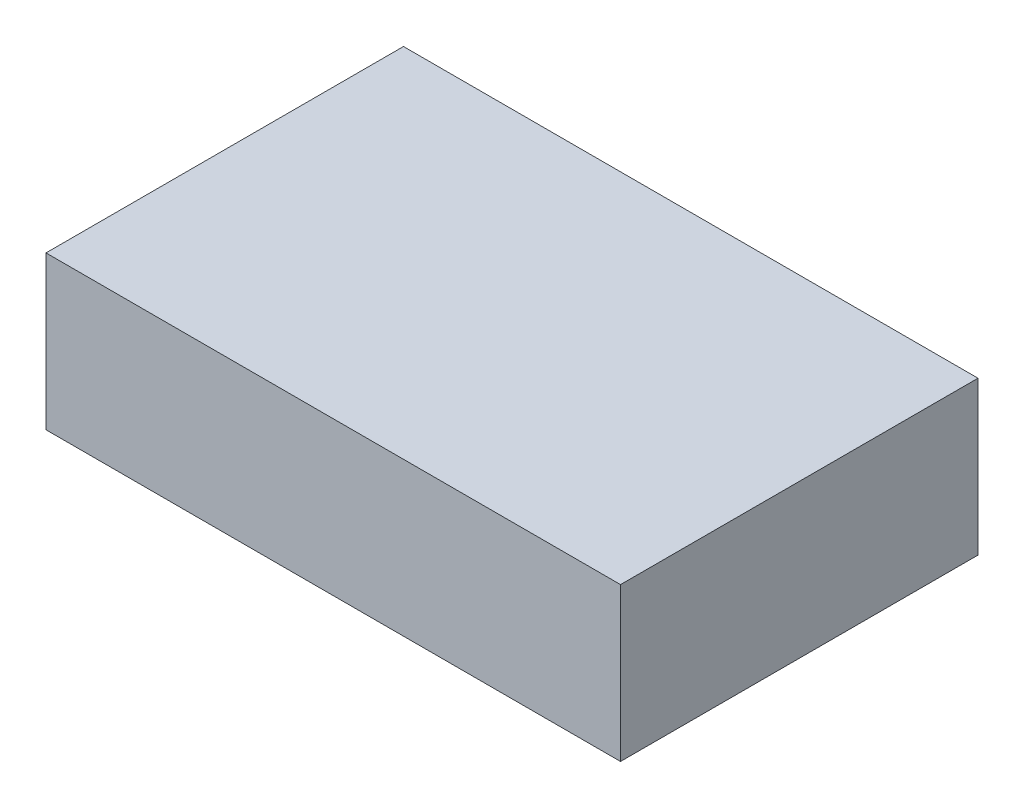
SolidWorks part; units mm, degrees
ref_plane "前视基准面" through (0, 0, 0) normal (0, 0, 1) x (1, 0, 0)
ref_plane "上视基准面" through (0, 0, 0) normal (0, 1, 0) x (1, 0, 0)
ref_plane "右视基准面" through (0, 0, 0) normal (1, 0, 0) x (0, 0, -1)
sketch "草图1" plane through (0, 0, 0) normal (0, 1, 0) x (1, 0, 0)
  line L1 (-45, 28) -> (45, 28)
  line L2 (-45, 28) -> (-45, -28)
  line L3 (-45, -28) -> (45, -28)
  line L4 (45, 28) -> (45, -28)
  line L5 (-45, 28) -> (45, -28) construction
  line L6 (-45, -28) -> (45, 28) construction
  point P0 (0, 0)
  dimension "D1" = 56
  dimension "D2" = 90
extrude "凸台-拉伸1" add sketch "草图1" along normal blind 24
sketch "草图2" plane through (0, 0, 0) normal (0, -1, 0) x (1, 0, 0)
  line L0 (-42, 25) -> (16, 25) construction
  line L1 (-45, -28) -> (-45, 28) construction
  line L2 (-45, 28) -> (45, 28) construction
  line L3 (0, 0) -> (-66.1012, 0) construction
  circle A0 centre (-42, 25) radius 1.5
  circle A1 centre (16, 25) radius 1.5
  circle A2 centre (16, -25) radius 1.5
  circle A3 centre (-42, -25) radius 1.5
  dimension "D1" = 3
  dimension "D2" = 3
  dimension "D3" = 58
  dimension "D4" = 3
  dimension "D5" = 3
extrude "切除-安装孔" cut sketch "草图2" against normal blind 10
